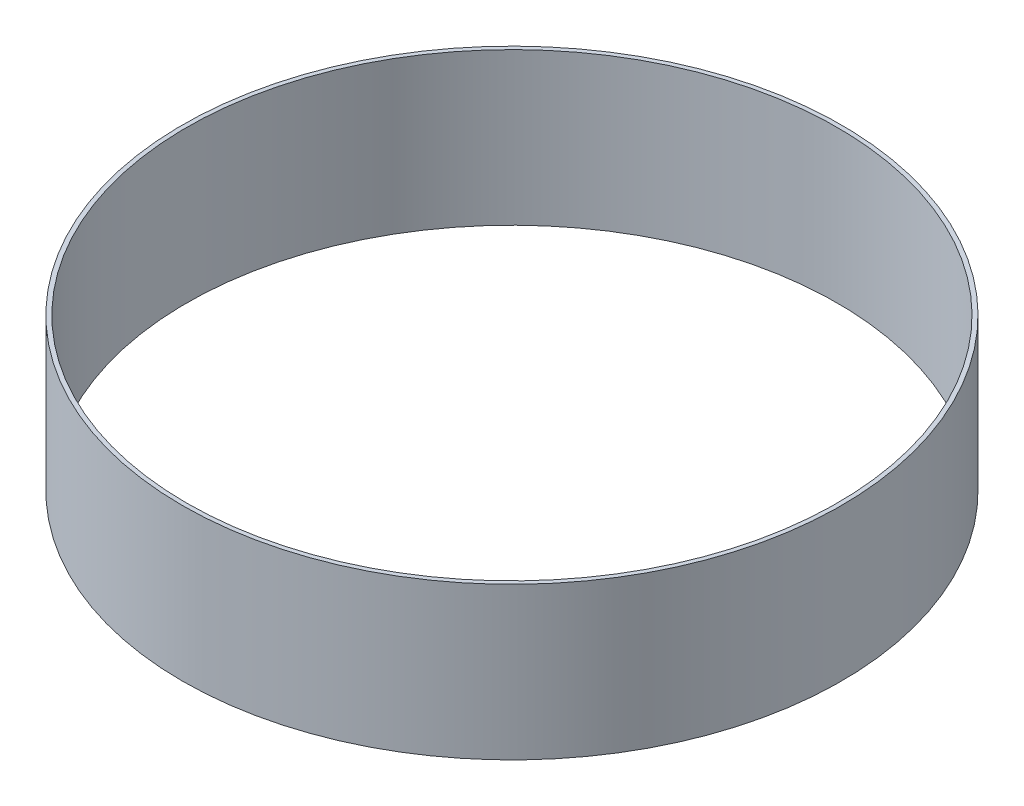
SolidWorks part; units mm, degrees
material "PC High Viscosity"
ref_plane "Front Plane" through (0, 0, 0) normal (0, 0, 1) x (1, 0, 0)
ref_plane "Top Plane" through (0, 0, 0) normal (0, 1, 0) x (1, 0, 0)
ref_plane "Right Plane" through (0, 0, 0) normal (1, 0, 0) x (0, 0, -1)
sketch "Sketch1" plane through (0, 0, 0) normal (0, 1, 0) x (1, 0, 0)
  circle A0 centre (0, 0) radius 247.65
  circle A1 centre (0, 0) radius 244.475
  dimension "D1" = 495.3
  dimension "D2" = 488.95
extrude "Boss-Extrude1" add sketch "Sketch1" along normal blind 114.3
